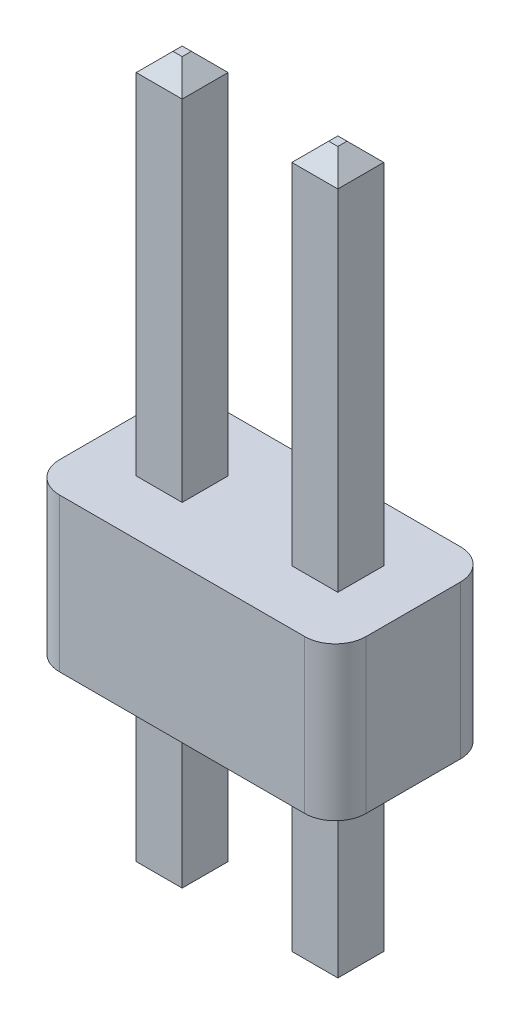
SolidWorks part; units mm, degrees
ref_plane "Front Plane" through (0, 0, 0) normal (0, 0, 1) x (1, 0, 0)
ref_plane "Top Plane" through (0, 0, 0) normal (0, 1, 0) x (1, 0, 0)
ref_plane "Right Plane" through (0, 0, 0) normal (1, 0, 0) x (0, 0, -1)
ref_plane "Plane1" through (0, 0, 0) normal (0, 1, 0) x (-1, 0, 0)
sketch "Sketch1" plane through (0, 0, 0) normal (0, 1, 0) x (-1, 0, 0)
  line L0 (-2, 1.27) -> (2, 1.27)
  line L1 (2.5, 0.77) -> (2.5, -0.77)
  line L2 (2, -1.27) -> (-2, -1.27)
  line L3 (-2.5, -0.77) -> (-2.5, 0.77)
  line L4 (0, 55) -> (0, -55) construction
  line L5 (55, 0) -> (-55, 0) construction
  arc A0 (2.5, 0.77) -> (2, 1.27) centre (2, 0.77) ccw
  arc A1 (2, -1.27) -> (2.5, -0.77) centre (2, -0.77) ccw
  arc A2 (-2.5, -0.77) -> (-2, -1.27) centre (-2, -0.77) ccw
  arc A3 (-2, 1.27) -> (-2.5, 0.77) centre (-2, 0.77) ccw
  dimension "D5" = 0.5
  dimension "D1" = 5
  dimension "D2" = 2.54
  dimension "D3" = 2.5
  dimension "D4" = 1.27
extrude "Boss-Extrude1" add sketch "Sketch1" along normal blind 2.5
ref_plane "Plane2" through (0, 0, 0) normal (0, 1, 0) x (-1, 0, 0)
sketch "Sketch2" plane through (0, 0, 0) normal (0, 1, 0) x (-1, 0, 0)
  line L0 (0.895, 0.375) -> (1.645, 0.375)
  line L1 (1.645, 0.375) -> (1.645, -0.375)
  line L2 (1.645, -0.375) -> (0.895, -0.375)
  line L3 (0.895, -0.375) -> (0.895, 0.375)
  line L4 (-0.895, -0.375) -> (-1.645, -0.375)
  line L5 (-1.645, -0.375) -> (-1.645, 0.375)
  line L6 (-1.645, 0.375) -> (-0.895, 0.375)
  line L7 (-0.895, 0.375) -> (-0.895, -0.375)
  line L8 (-1.645, 0.375) -> (-0.895, -0.375) construction
  line L9 (0.895, -0.375) -> (1.645, 0.375) construction
  line L10 (1.375, 0) -> (-1.375, 0) construction
  line L11 (0, 1.375) -> (0, -1.375) construction
  point P8 (-1.27, 0)
  point P9 (1.27, 0)
  dimension "D1" = 2.54
  dimension "D2" = 0.75
  dimension "D3" = 1.27
extrude "Boss-Extrude2" add sketch "Sketch2" along normal blind 8.5 and the other way blind 3.25
chamfer "Chamfer1" distance 0.3 angle 45 16 edges at (-1.645, 8.5, 0) (-1.27, 8.5, -0.375) (-0.895, 8.5, 0) (-1.27, 8.5, 0.375) (0.895, 8.5, 0) (1.27, 8.5, -0.375) (1.645, 8.5, 0) (1.27, 8.5, 0.375) (1.27, -3.25, -0.375) (1.645, -3.25, 0) (0.895, -3.25, 0) (1.27, -3.25, 0.375) (-1.27, -3.25, 0.375) (-1.645, -3.25, 0) (-0.895, -3.25, 0) (-1.27, -3.25, -0.375)
